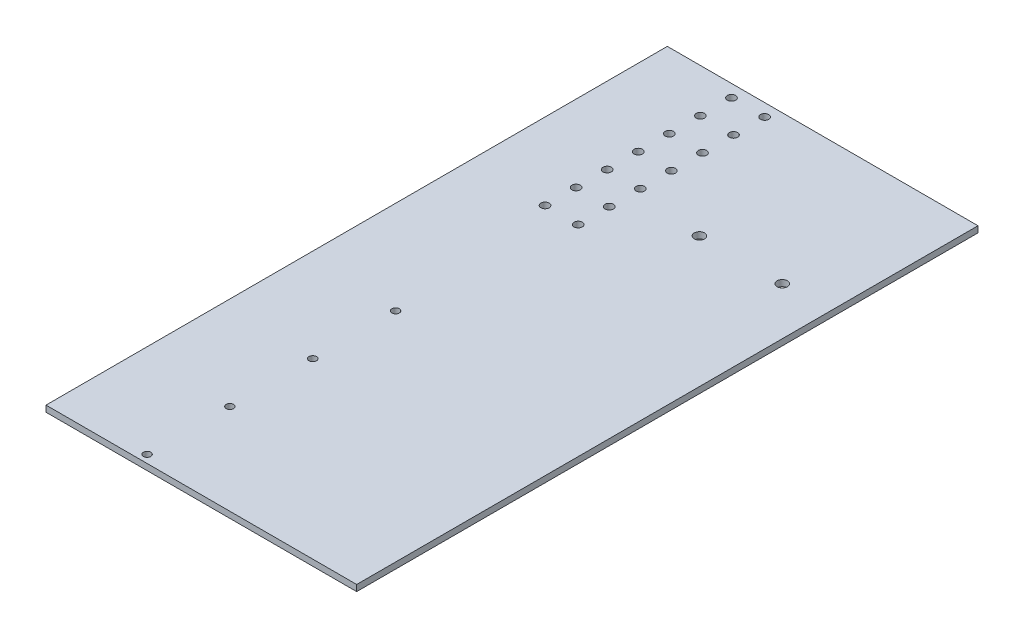
SolidWorks part; units mm, degrees
ref_plane "Front Plane" through (0, 0, 0) normal (0, 0, 1) x (1, 0, 0)
ref_plane "Top Plane" through (0, 0, 0) normal (0, 1, 0) x (1, 0, 0)
ref_plane "Right Plane" through (0, 0, 0) normal (1, 0, 0) x (0, 0, -1)
sketch "Sketch1" plane through (0, 0, 0) normal (0, 1, 0) x (1, 0, 0)
  line L1 (-75, -150) -> (75, -150)
  line L2 (-75, -150) -> (-75, 150)
  line L3 (-75, 150) -> (75, 150)
  line L4 (75, -150) -> (75, 150)
  line L5 (-75, -150) -> (75, 150) construction
  line L6 (-75, 150) -> (75, -150) construction
  point P0 (0, 0)
  dimension "D1" = 300
  dimension "D2" = 150
extrude "Boss-Extrude1" add sketch "Sketch1" along normal blind 3
sketch "Sketch2" plane through (0, 0, 0) normal (0, -1, 0) x (1, 0, 0)
  circle A0 centre (52, -78.5) radius 2.5
  circle A1 centre (12, -78.5) radius 2.5
  dimension "D1" = 5
extrude "Cut-Extrude1" cut sketch "Sketch2" against normal blind 10
sketch "Sketch3" plane through (0, 3, 0) normal (0, 1, 0) x (1, 0, 0)
  circle A0 centre (-30.006, -146.2) radius 1.8
  circle A1 centre (-30.006, -106.2) radius 1.8
  circle A2 centre (-30.006, -66.2) radius 1.8
  circle A3 centre (-30.006, -26.2) radius 1.8
  dimension "D1" = 3.6
extrude "Cut-Extrude2" cut sketch "Sketch3" against normal blind 10
sketch "Sketch4" plane through (0, 3, 0) normal (0, 1, 0) x (1, 0, 0)
  circle A0 centre (-38.006, 53.9681) radius 2
  circle A1 centre (-22.006, 53.9681) radius 2
  dimension "D1" = 4
extrude "Cut-Extrude3" cut sketch "Sketch4" against normal blind 8.5
sketch "Sketch5" plane through (0, 3, 0) normal (0, 1, 0) x (1, 0, 0)
  line L0 (-38.006, 53.9681) -> (-38.006, 150) construction
  line L1 (75, 150) -> (-75, 150) construction
  line L2 (-22.006, 53.9681) -> (-22.006, 150) construction
  line L3 (-38.006, 68.9681) -> (-22.006, 68.9681) construction
  circle A0 centre (-38.006, 68.9681) radius 2
  circle A1 centre (-22.006, 68.9681) radius 2
  circle A2 centre (-38.006, 83.9681) radius 2
  circle A3 centre (-22.006, 83.9681) radius 2
  circle A4 centre (-38.006, 98.9681) radius 2
  circle A5 centre (-22.006, 98.9681) radius 2
  circle A6 centre (-38.006, 113.9681) radius 2
  circle A7 centre (-22.006, 113.9681) radius 2
  circle A8 centre (-38.006, 128.9681) radius 2
  circle A9 centre (-22.006, 128.9681) radius 2
  circle A10 centre (-38.006, 143.9681) radius 2
  circle A11 centre (-22.006, 143.9681) radius 2
  dimension "D1" = 4
  dimension "D2" = 15
  dimension "D4" = 15
  dimension "D3" = 6
extrude "Cut-Extrude4" cut sketch "Sketch5" against normal blind 10
